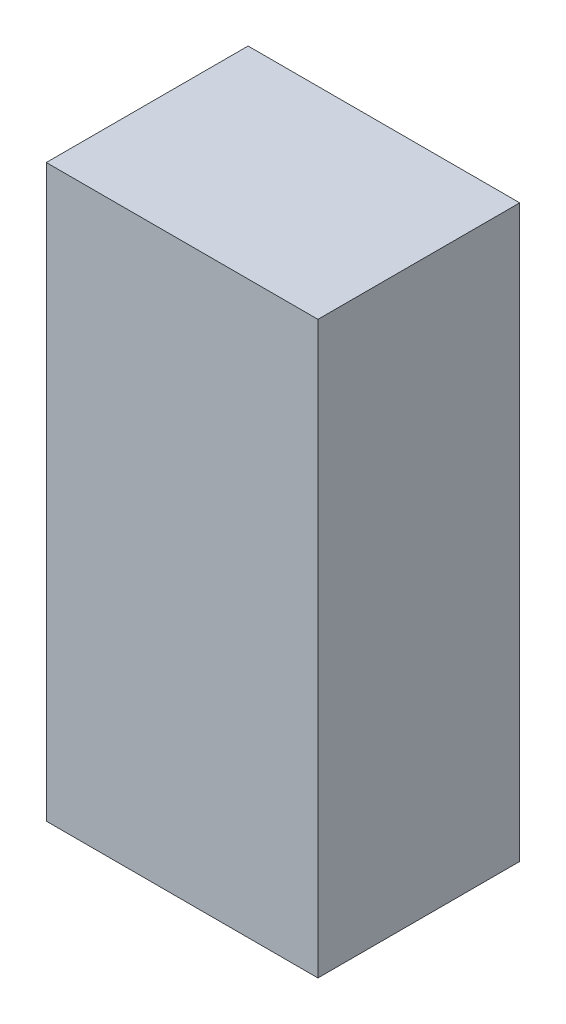
SolidWorks part; units mm, degrees
ref_plane "Alzado" through (0, 0, 0) normal (0, 0, 1) x (1, 0, 0)
ref_plane "Planta" through (0, 0, 0) normal (0, 1, 0) x (1, 0, 0)
ref_plane "Vista lateral" through (0, 0, 0) normal (1, 0, 0) x (0, 0, -1)
sketch "Croquis1" plane through (0, 0, 0) normal (0, 1, 0) x (1, 0, 0)
  line L1 (-17.5, -13) -> (17.5, -13)
  line L2 (-17.5, -13) -> (-17.5, 13)
  line L3 (-17.5, 13) -> (17.5, 13)
  line L4 (17.5, -13) -> (17.5, 13)
  line L5 (-17.5, -13) -> (17.5, 13) construction
  line L6 (-17.5, 13) -> (17.5, -13) construction
  point P0 (0, 0)
  dimension "D1" = 35
  dimension "D2" = 26
extrude "Saliente-Extruir1" add sketch "Croquis1" along normal blind 73.5
